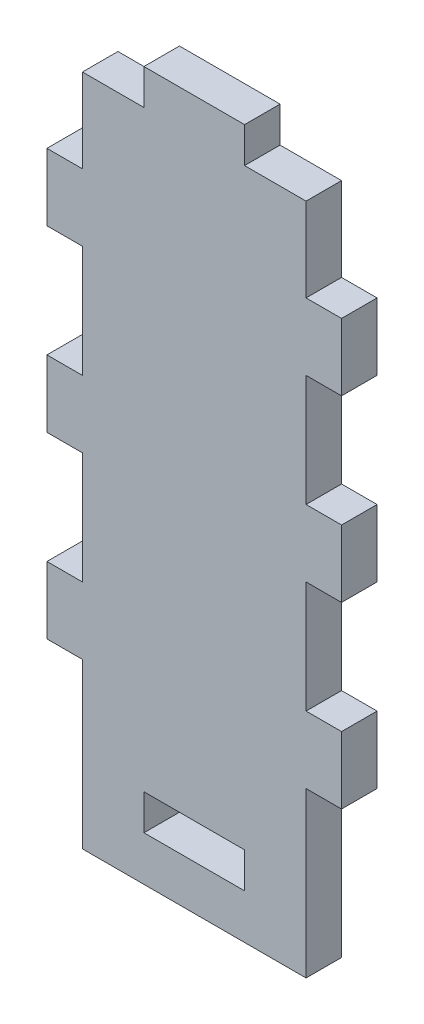
SolidWorks part; units mm, degrees
ref_plane "Front Plane" through (0, 0, 0) normal (0, 0, 1) x (1, 0, 0)
ref_plane "Top Plane" through (0, 0, 0) normal (0, 1, 0) x (1, 0, 0)
ref_plane "Right Plane" through (0, 0, 0) normal (1, 0, 0) x (0, 0, -1)
sketch "Sketch1" plane through (0, 0, 0) normal (0, 0, 1) x (1, 0, 0)
  line L0 (-5.5, 7.175) -> (0, 7.175) construction
  line L1 (0, 14.675) -> (3.175, 14.675)
  line L2 (3.175, 14.675) -> (3.175, 20.675)
  line L3 (3.175, 20.675) -> (0, 20.675)
  line L4 (0, 20.675) -> (0, 30.675)
  line L5 (0, 30.675) -> (3.175, 30.675)
  line L6 (3.175, 30.675) -> (3.175, 36.675)
  line L7 (3.175, 36.675) -> (0, 36.675)
  line L8 (0, 36.675) -> (0, 46.675)
  line L9 (0, 46.675) -> (3.175, 46.675)
  line L10 (3.175, 46.675) -> (3.175, 52.675)
  line L11 (3.175, 52.675) -> (0, 52.675)
  line L12 (0, 52.675) -> (0, 60.175)
  line L13 (0, 60.175) -> (-5.5, 60.175)
  line L14 (-5.5, 60.175) -> (-5.5, 63.35)
  line L15 (-5.5, 63.35) -> (-14.5, 63.35)
  line L16 (-14.5, 63.35) -> (-14.5, 60.175)
  line L17 (-14.5, 60.175) -> (-20, 60.175)
  line L18 (3.175, 30.0875) -> (-38.4558, 30.0875) construction
  line L19 (-10, 61.175) -> (-10, 29) construction
  line L20 (-20, 52.675) -> (-20, 60.175)
  line L21 (-23.175, 52.675) -> (-20, 52.675)
  line L22 (-23.175, 46.675) -> (-23.175, 52.675)
  line L23 (-20, 46.675) -> (-23.175, 46.675)
  line L24 (-20, 36.675) -> (-20, 46.675)
  line L25 (-23.175, 36.675) -> (-20, 36.675)
  line L26 (-23.175, 30.675) -> (-23.175, 36.675)
  line L27 (-20, 30.675) -> (-23.175, 30.675)
  line L28 (-20, 20.675) -> (-20, 30.675)
  line L29 (-23.175, 20.675) -> (-20, 20.675)
  line L30 (-23.175, 14.675) -> (-23.175, 20.675)
  line L31 (-20, 14.675) -> (-23.175, 14.675)
  line L32 (-14.5, 7.175) -> (-20, 7.175) construction
  line L33 (-20, 0) -> (0, 0)
  line L34 (-10, 0) -> (-10, 4)
  line L35 (-5.5, 4) -> (-5.5, 7.175)
  line L36 (-5.5, 7.175) -> (-14.5, 7.175)
  line L37 (-5.5, 4) -> (-14.5, 4)
  line L38 (-14.5, 4) -> (-14.5, 7.175)
  line L39 (-20, 7.175) -> (-20, 14.675)
  line L40 (-20, 7.175) -> (-20, 0)
  line L41 (0, 7.175) -> (0, 14.675)
  line L42 (0, 7.175) -> (0, 0)
  point P44 (-10, 7.175)
  dimension "D1" = 4
  dimension "D2" = 3.175
  dimension "D3" = 6
  dimension "D4" = 10
  dimension "D5" = 9
  dimension "D6" = 3.175
  dimension "D7" = 20
  dimension "D8" = 3.175
  dimension "D9" = 9
  dimension "D10" = 53
extrude "Boss-Extrude2" add sketch "Sketch1" along normal mid plane 3.175
